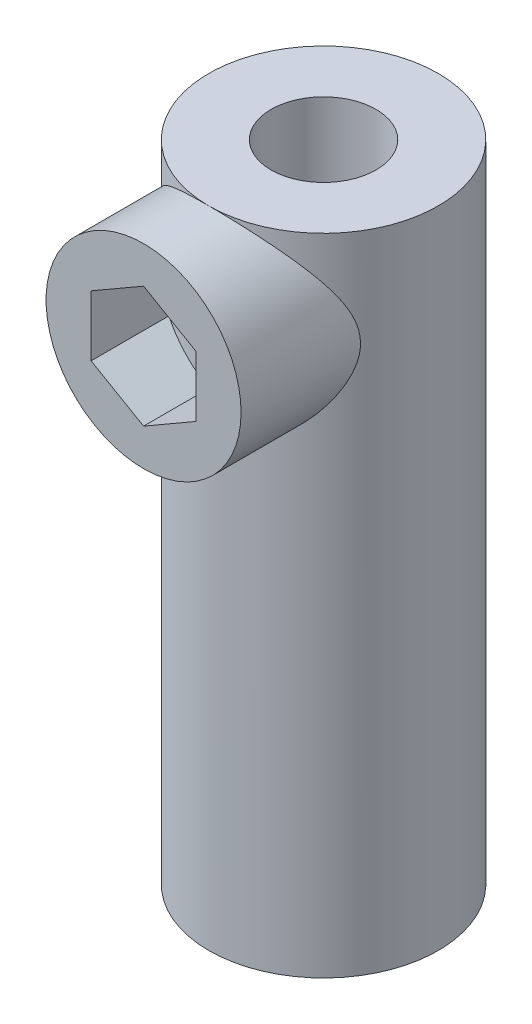
SolidWorks part; units mm, degrees
ref_plane "Alzado" through (0, 0, 0) normal (0, 0, 1) x (1, 0, 0)
ref_plane "Planta" through (0, 0, 0) normal (0, 1, 0) x (1, 0, 0)
ref_plane "Vista lateral" through (0, 0, 0) normal (1, 0, 0) x (0, 0, -1)
sketch "Croquis1" plane through (0, 0, 0) normal (0, 1, 0) x (1, 0, 0)
  line L0 (0, 93.8671) -> (0, -75) construction
  line L1 (-140.5381, 0) -> (179.4923, 0) construction
  arc A1 (-18.6295, 70.7338) -> (18.6295, 70.7338) centre (0, 67) ccw
  arc A2 (-18.6295, 70.7338) -> (-29.224, 79.8183) centre (-26.4735, 72.306) ccw
  arc A3 (18.6295, 70.7338) -> (29.224, 79.8183) centre (26.4735, 72.306) cw
  arc A4 (51.9425, 51.5005) -> (54.5127, 65.2179) centre (49.3821, 59.0797) ccw
  arc A5 (51.9425, 51.5005) -> (70.572, 19.2333) centre (58.0237, 33.5) ccw
  arc A6 (70.572, 19.2333) -> (83.7367, 14.6004) centre (75.8556, 13.2263) cw
  arc A7 (70.572, -19.2333) -> (83.7367, -14.6004) centre (75.8556, -13.2263) ccw
  arc A8 (70.572, -19.2333) -> (51.9425, -51.5005) centre (58.0237, -33.5) ccw
  arc A9 (51.9425, -51.5005) -> (54.5127, -65.2179) centre (49.3821, -59.0797) cw
  arc A10 (18.6295, -70.7338) -> (29.224, -79.8183) centre (26.4735, -72.306) ccw
  arc A11 (18.6295, -70.7338) -> (-18.6295, -70.7338) centre (0, -67) ccw
  arc A12 (-18.6295, -70.7338) -> (-29.224, -79.8183) centre (-26.4735, -72.306) cw
  arc A13 (-51.9425, -51.5005) -> (-54.5127, -65.2179) centre (-49.3821, -59.0797) ccw
  arc A14 (-51.9425, -51.5005) -> (-70.572, -19.2333) centre (-58.0237, -33.5) ccw
  arc A15 (-70.572, -19.2333) -> (-83.7367, -14.6004) centre (-75.8556, -13.2263) cw
  arc A16 (-70.572, 19.2333) -> (-83.7367, 14.6004) centre (-75.8556, 13.2263) ccw
  arc A17 (-70.572, 19.2333) -> (-51.9425, 51.5005) centre (-58.0237, 33.5) ccw
  arc A18 (-51.9425, 51.5005) -> (-54.5127, 65.2179) centre (-49.3821, 59.0797) cw
  arc A26 (-54.5127, -65.2179) -> (-29.224, -79.8183) centre (0, 0) ccw
  arc A27 (-83.7367, 14.6004) -> (-83.7367, -14.6004) centre (0, 0) ccw
  arc A28 (-54.5127, -65.2179) -> (-29.224, -79.8183) centre (0, 0) ccw
  arc A29 (29.224, -79.8183) -> (54.5127, -65.2179) centre (0, 0) ccw
  arc A30 (54.5127, 65.2179) -> (29.224, 79.8183) centre (0, 0) ccw
  arc A31 (83.7367, -14.6004) -> (83.7367, 14.6004) centre (0, 0) ccw
  arc A32 (54.5127, 65.2179) -> (29.224, 79.8183) centre (0, 0) ccw
  arc A33 (-29.224, 79.8183) -> (-54.5127, 65.2179) centre (0, 0) ccw
  arc A34 (29.224, -79.8183) -> (54.5127, -65.2179) centre (0, 0) ccw
  arc A35 (83.7367, -14.6004) -> (83.7367, 14.6004) centre (0, 0) ccw
  circle A38 centre (0, 0) radius 7.65
  point P14 (58.0237, -33.5)
  point P15 (58.0237, 33.5)
  point P19 (0, -67)
  point P21 (-58.0237, -33.5)
  point P25 (-58.0237, 33.5)
  point P27 (-49.3821, 59.0797)
  point P31 (-26.4735, 72.306)
  point P33 (49.3821, 59.0797)
  point P37 (26.4735, 72.306)
  point P39 (75.8556, 13.2263)
  point P46 (75.8556, -13.2263)
  point P48 (49.3821, -59.0797)
  point P52 (26.4735, -72.306)
  point P54 (-26.4735, -72.306)
  point P55 (-49.3821, -59.0797)
  point P56 (-75.8556, 13.2263)
  point P57 (-75.8556, -13.2263)
  point P58 (0, 0)
  dimension "D1" = 85
  dimension "D2" = 38
  dimension "D3" = 6
  dimension "D4" = 8
  dimension "D5" = 15.3
  dimension "D6" = 67
extrude "Saliente-Extruir1" add sketch "Croquis1" along normal mid plane 17 contours A2 A33 A18 A17 A16 A27 A15 A14 A13 A26 A12 A11 A10 A29 A9 A8 A7 A31 A6 A5 A4 A30 A3 A1 A38
sketch "Croquis2" plane through (0, 0, 0) normal (0, 1, 0) x (1, 0, 0)
  circle A2 centre (0, 0) radius 3.5
  circle A3 centre (0, 0) radius 7.65 construction
  circle A4 centre (0, 0) radius 7.65
  dimension "D1" = 7
extrude "Saliente-Extruir2" add sketch "Croquis2" along normal blind 21.5 separate body
mirror "Simetría3" about plane through (0, 0, 0) normal (0, 1, 0) of bodies 102
sketch "Croquis3" plane through (0, 0, 0) normal (0, 0, 1) x (1, 0, 0)
  line L0 (7.65, 21.5) -> (-7.65, 21.5) construction
  line L1 (0, 10.9585) -> (3.5, 12.9793)
  line L2 (3.5, 12.9793) -> (3.5, 17.0207)
  line L3 (3.5, 17.0207) -> (0, 19.0415)
  line L4 (0, 19.0415) -> (-3.5, 17.0207)
  line L5 (-3.5, 17.0207) -> (-3.5, 12.9793)
  line L6 (-3.5, 12.9793) -> (0, 10.9585)
  line L8 (0, 15) -> (0, 21.5) construction
  line L10 (19, 8.5) -> (-19, 8.5) construction
  circle A0 centre (0, 15) radius 3.5 construction
  circle A1 centre (0, 15) radius 6.5
  dimension "D1" = 7
  dimension "D2" = 3
extrude "Saliente-Extruir3" add sketch "Croquis3" against normal up to next from offset 12
sketch "Croquis4" plane through (0, 0, 12) normal (0, 0, 1) x (1, 0, 0)
  circle A0 centre (0, 15) radius 2.25
  dimension "D1" = 4.5
extrude "Cortar-Extruir1" cut sketch "Croquis4" against normal up to next
delete or keep bodies "Sólido-Eliminar/Conservar 1" [suppressed] type delete bodies bodies 105
delete or keep bodies "Sólido-Eliminar/Conservar 2" type delete bodies bodies 101
